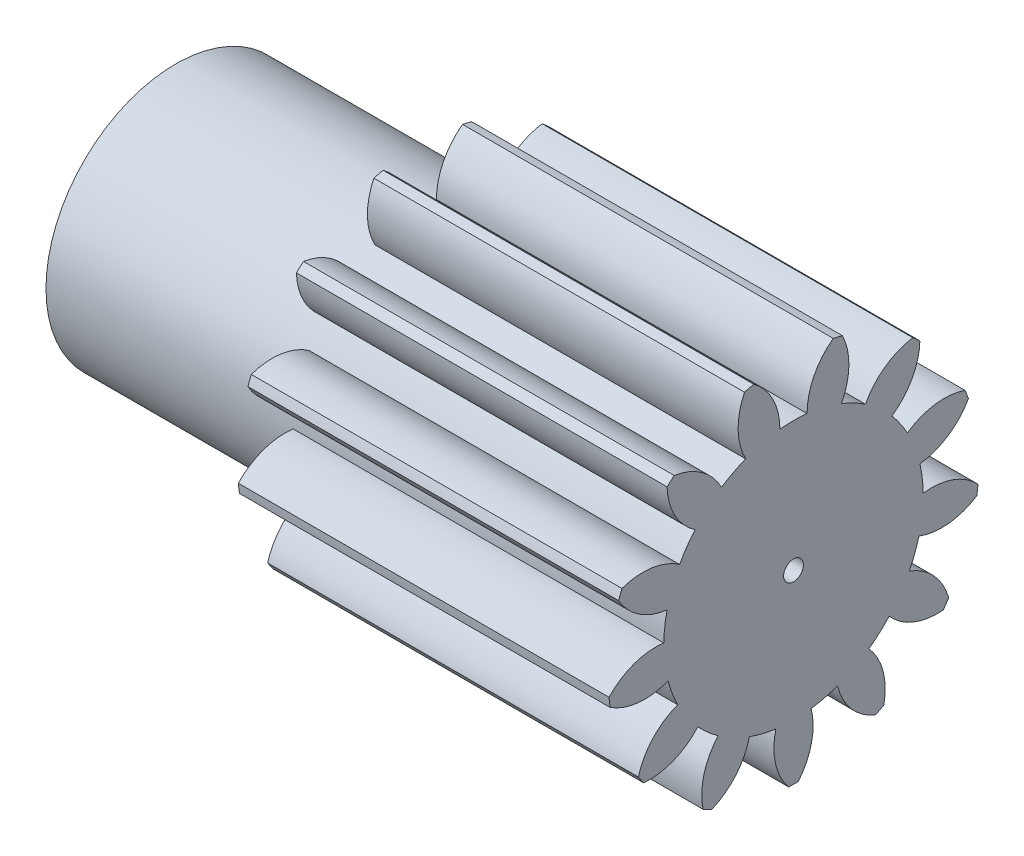
SolidWorks part; units mm, degrees
ref_plane "Plane1" through (0, 0, 0) normal (0, 0, 1) x (1, 0, 0)
ref_plane "Plane2" through (0, 0, 0) normal (0, 1, 0) x (1, 0, 0)
ref_plane "Plane3" through (0, 0, 0) normal (1, 0, 0) x (0, 0, -1)
sketch "HoldingSke" plane through (0, 0, 0) normal (0, 1, 0) x (1, 0, 0)
  line L0 (0, 0) -> (0.9744, -0.225)
  line L1 (-15, 0) -> (100, 0) construction
  line L2 (0, 0) -> (-2.1039, 2.3779)
  line L3 (0, 0) -> (-11.863, 4.5341)
  line L4 (0, 0) -> (8.4147, 1.9427)
  line L5 (0, 0) -> (-23.4238, -8.7364)
  line L6 (0, 0) -> (-12.4344, -8.3896)
  line L7 (-2.1039, 2.3779) -> (3.2774, 26.7919)
  line L8 (-76.2, 54.61) -> (-76.1, 54.61)
  line L9 (-71.009, 38.7566) -> (-53.1078, 45.2721)
  line L10 (-76.2, 71.12) -> (104.1128, 71.12)
  line L11 (0, 0) -> (-15, 0)
  line L12 (-76.2, 101.6) -> (-76.162, 101.6)
  line L13 (24.9733, 27.94) -> (52.9518, 28.4284)
  line L14 (24.9733, 27.94) -> (24.9743, 27.94)
  line L15 (24.9733, 27.94) -> (100.4006, 29.5858)
  line L16 (-63.627, -1) -> (-12.827, -1)
  circle A0 centre (0, 0) radius 0.4
  circle A1 centre (0, 0) radius 5.249
  circle A2 centre (0, 0) radius 37.5
  circle A3 centre (0, 0) radius 0.4
  dimension "MHD" = 10.498
  dimension "Hub_dia" = 75
  dimension "Num_teeth" = 13
  dimension "Pitch" = 1
  dimension "Show_teeth" = 13
  dimension "Thickness" = 15
  dimension "Ap" = 20
  dimension "H" = 19.05
  dimension "Pitch_radius" = 180.3128
  dimension "Width" = 15
  dimension "Backlash" = 0.038
  dimension "Addendum_fac" = 1
  dimension "Dedendum_fac" = 1.25
  dimension "Clearance_fac" = 0.25
  dimension "Dedendum_add" = 0.001
  dimension "Module" = 1
sketch "BasProSke" plane through (0, 0, 0) normal (0, 1, 0) x (1, 0, 0)
  line L0 (-10, 0) -> (60, 0) construction
  line L1 (0, 0) -> (0, 7.5)
  line L2 (0, 0) -> (15, 0)
  line L3 (15, 0) -> (15, 7.5)
  line L4 (15, 7.5) -> (0, 7.5)
  dimension "Thickness" = 15
  dimension "Diameter" = 15
revolve "Base-Revolve" add sketch "BasProSke" angle 360 about L0
sketch "TooCutSke" plane through (0, 0, 0) normal (1, 0, 0) x (0, 0, -1)
  line L1 (0, 0) -> (0, 107) construction
  line L2 (0, 0) -> (-0.8499, 6.4442) construction
  line L3 (0, 0) -> (-3.0921, 12.5452) construction
  line L4 (-0.8499, 6.4442) -> (-1.5461, 6.2726) construction
  arc A0 (0.5505, 5.2201) -> (-0.5505, 5.2201) centre (0, 0) ccw
  arc A1 (1.6352, 7.3456) -> (-1.6352, 7.3456) centre (0, 0) ccw
  circle A2 centre (0, 0) radius 6.5 construction
  circle A3 centre (0, 0) radius 6.108 construction
  arc A4 (-0.5505, 5.2201) -> (-1.6352, 7.3456) centre (-3.1505, 5.2328) ccw
  arc A5 (1.6352, 7.3456) -> (0.5505, 5.2201) centre (3.1505, 5.2328) ccw
  dimension "Root_dia" = 10.498
  dimension "Overcut_dia" = 15.0508
  dimension "Pitch_dia" = 13
  dimension "Base_dia" = 12.216
  dimension "Flank_rad" = 2.6
  dimension "Half_ang" = 13.846
  dimension "Half_CT" = 0.717
extrude "ToothCut" cut sketch "TooCutSke" along normal through all
fillet "Breaks" [suppressed] radius 0.02
fillet "RootFillets" [suppressed] radius 0.251
pattern_circular "TeethCuts" count 13 every 27.692 about axis through (-10, 0, 0) along (1, 0, 0) of "ToothCut", "RootFillets", "Breaks"
sketch "HubNeaOneSke" plane through (0, 0, 0) normal (-1, 0, 0) x (0, 0, 1)
  circle A0 centre (0, 0) radius 5.249
  dimension "Diameter" = 10.498
extrude "HubNearOne" add sketch "HubNeaOneSke" along normal blind 10.0001
sketch "HubNeaBotSke" plane through (0, 0, 0) normal (-1, 0, 0) x (0, 0, 1)
  circle A0 centre (0, 0) radius 5.249
  dimension "Diameter" = 10.498
extrude "HubNearBoth" [suppressed] add sketch "HubNeaBotSke" along normal blind 5
ref_plane "FarPln" through (15, 0, 0) normal (1, 0, 0) x (0, 0, -1)
sketch "HubFarSke" plane through (15, 0, 0) normal (1, 0, 0) x (0, 0, -1)
  circle A0 centre (0, 0) radius 5.249
  dimension "Diameter" = 10.498
extrude "HubFar" [suppressed] add sketch "HubFarSke" along normal blind 5
sketch "BorSke" plane through (0, 0, 0) normal (1, 0, 0) x (0, 0, -1)
  circle A0 centre (0, 0) radius 0.4
extrude "Bore" cut sketch "BorSke" along normal mid plane 50.0001
sketch "KeySke" plane through (0, 0, 0) normal (1, 0, 0) x (0, 0, -1)
  line L0 (-0.05, 0) -> (-0.05, 0.5)
  line L1 (-0.05, 0.5) -> (0.05, 0.5)
  line L2 (0.05, 0.5) -> (0.05, 0)
  line L3 (0, 0) -> (0, 34) construction
  line L4 (-0.05, 0) -> (0.05, 0)
extrude "Keyway" [suppressed] cut sketch "KeySke" along normal mid plane 50.0001
pattern_circular "Keyway2" [suppressed] count 2 every 90 about axis through (-10, 0, 0) along (1, 0, 0)
equation "' \"Module@HoldingSke\" = 6.35"
equation "' \"Num_teeth@HoldingSke\" = 12"
equation "' \"Ap@HoldingSke\" =  20"
equation "' \"Ap@HoldingSke\" = 20"
equation "' \"Width@HoldingSke\" = 0.5 * 25.4"
equation "' \"Hub_dia@HoldingSke\"= 1 * 25.4"
equation "' \"Hub_dia@HoldingSke\" = 1 * 25.4"
equation "' \"Overall_len@HoldingSke\" = 1.0 * 25.4"
equation "' \"Bore@HoldingSke\" = 0.75 * 25.4"
equation "' \"T_dim@HoldingSke\" = 0.1 * 25.4"
equation "' \"Width@KeySke\" = 0.25 * 25.4"
equation "' \"Show_teeth@HoldingSke\" = 13"
equation "' \"Backlash@HoldingSke\" = 0.009 * 25.4"
equation "' \"Addendum_fac@HoldingSke\" = 1.0"
equation "' \"Dedendum_fac@HoldingSke\" = 1.25"
equation "' \"Dedendum_add@HoldingSke\" = 0.00005 * 25.4"
equation "' \"Clearance_fac@HoldingSke\" = 0.25"
equation "\"Pitch@HoldingSke\" = 1 / \"Module@HoldingSke\""
equation "\"Overcut_dia@TooCutSke\" = (\"Num_teeth@HoldingSke\" + 2 * \"Addendum_fac@HoldingSke\") / \"Pitch@HoldingSke\" + 0.002 * 25.4"
equation "\"Pitch_dia@TooCutSke\" = \"Num_teeth@HoldingSke\" / \"Pitch@HoldingSke\""
equation "\"Base_dia@TooCutSke\" = \"Num_teeth@HoldingSke\" / \"Pitch@HoldingSke\" * cos((\"Ap@HoldingSke\"  * 3.14159265 / 180))"
equation "\"Root_dia@TooCutSke\" = (\"Num_teeth@HoldingSke\" + 2) / \"Pitch@HoldingSke\" - 2 * (\"Addendum_fac@HoldingSke\" + \"Dedendum_fac@HoldingSke\") / \"Pitch@HoldingSke\" - \"Dedendum_add@HoldingSke\" * 2"
equation "\"Half_ang@TooCutSke\" = 180 / \"Num_teeth@HoldingSke\""
equation "\"Half_CT@TooCutSke\" = \"Num_teeth@HoldingSke\" / \"Pitch@HoldingSke\" * sin((3.14159265 / 2 / \"Num_teeth@HoldingSke\")) / 2 - 7 * \"Backlash@HoldingSke\" / 4"
equation "\"Flank_rad@TooCutSke\" = \"Num_teeth@HoldingSke\" / \"Pitch@HoldingSke\" / 5"
equation "\"Radius@RootFillets\" = \"Clearance_fac@HoldingSke\" / \"Pitch@HoldingSke\" + \"Dedendum_add@HoldingSke\""
equation "\"Break_rad@Breaks\" = 0.02 / \"Pitch@HoldingSke\""
equation "\"Thickness@HoldingSke\" = \"Width@HoldingSke\""
equation "\"OAL@HoldingSke\" = \"Thickness@HoldingSke\""
equation "\"MHD@HoldingSke\" = (\"Num_teeth@HoldingSke\" + 2) / \"Pitch@HoldingSke\" - 2 * (\"Addendum_fac@HoldingSke\" + \"Dedendum_fac@HoldingSke\")  / \"Pitch@HoldingSke\" - \"Dedendum_add@HoldingSke\" * 2"
equation "\"MBD@HoldingSke\" = (\"Num_teeth@HoldingSke\" + 2) / \"Pitch@HoldingSke\" - 2 * (\"Addendum_fac@HoldingSke\" + \"Dedendum_fac@HoldingSke\")  / \"Pitch@HoldingSke\" - \"Dedendum_add@HoldingSke\" * 2 - 0.002 * 25.4"
equation "\"MHD@HoldingSke\" = ((sgn( \"MHD@HoldingSke\" - \"Hub_dia@HoldingSke\" )-1)*( \"MHD@HoldingSke\" - \"Hub_dia@HoldingSke\" ))/-2+ \"Hub_dia@HoldingSke\""
equation "\"MBD@HoldingSke\" = ((sgn( \"MBD@HoldingSke\" - \"Bore@HoldingSke\" )-1)*( \"MBD@HoldingSke\" - \"Bore@HoldingSke\" ))/-2+ \"Bore@HoldingSke\""
equation "\"OAL@HoldingSke\" = ((sgn( \"OAL@HoldingSke\" - \"Overall_len@HoldingSke\" )+1)*( \"OAL@HoldingSke\" - \"Overall_len@HoldingSke\" ))/2 + \"Overall_len@HoldingSke\" + 0.000002 * 25.4"
equation "\"Num_teeth@TeethCuts\" = int( \"Show_teeth@HoldingSke\" ) + 1"
equation "\"Num_teeth@TeethCuts\" = ((sgn( \"Num_teeth@TeethCuts\" - \"Num_teeth@HoldingSke\" )-1)*( \"Num_teeth@TeethCuts\" - \"Num_teeth@HoldingSke\" ))/-2+ \"Num_teeth@HoldingSke\""
equation "\"Num_teeth@TeethCuts\" = ((sgn( \"Num_teeth@TeethCuts\" - 2.0)+1)*( \"Num_teeth@TeethCuts\" - 2.0))/2 +2.0"
equation "\"Angle@TeethCuts\" = 360.0 / \"Num_teeth@HoldingSke\""
equation "\"Diameter@BasProSke\" = (\"Num_teeth@HoldingSke\" + 2 * \"Addendum_fac@HoldingSke\") / \"Pitch@HoldingSke\""
equation "\"Thickness@BasProSke\"  = \"Thickness@HoldingSke\""
equation "' \"Fillet_rad@BasProSke\" =  \"Thickness@HoldingSke\" * 0.05"
equation "' \"Fillet_rad@BasProSke\" = \"Thickness@HoldingSke\" * 0.05"
equation "\"MHD@HoldingSke\" = ((sgn( \"MHD@HoldingSke\" - \"Root_dia@TooCutSke\" )-1)*( \"MHD@HoldingSke\" - \"Root_dia@TooCutSke\" ))/-2+ \"Root_dia@TooCutSke\""
equation "\"Diameter@HubNeaOneSke\" = \"MHD@HoldingSke\""
equation "\"Length@HubNearOne\" = \"OAL@HoldingSke\" - \"Thickness@BasProSke\""
equation "\"Diameter@HubNeaBotSke\" = \"MHD@HoldingSke\""
equation "\"Length@HubNearBoth\" = ( \"OAL@HoldingSke\" - \"Thickness@BasProSke\" ) / 2.0"
equation "\"Thickness@FarPln\" = \"Thickness@BasProSke\""
equation "\"Diameter@HubFarSke\" = \"MHD@HoldingSke\""
equation "\"Length@HubFar\" = ( \"OAL@HoldingSke\" - \"Thickness@BasProSke\" ) / 2.0"
equation "\"Diameter@BorSke\" = \"MBD@HoldingSke\""
equation "\"D1@Bore\" = \"OAL@HoldingSke\" * 2.0"
equation "\"D1@Keyway\" = \"OAL@HoldingSke\" * 2.0"
equation "\"Offset@KeySke\" = \"T_dim@HoldingSke\" + \"MBD@HoldingSke\" / 2.0"
